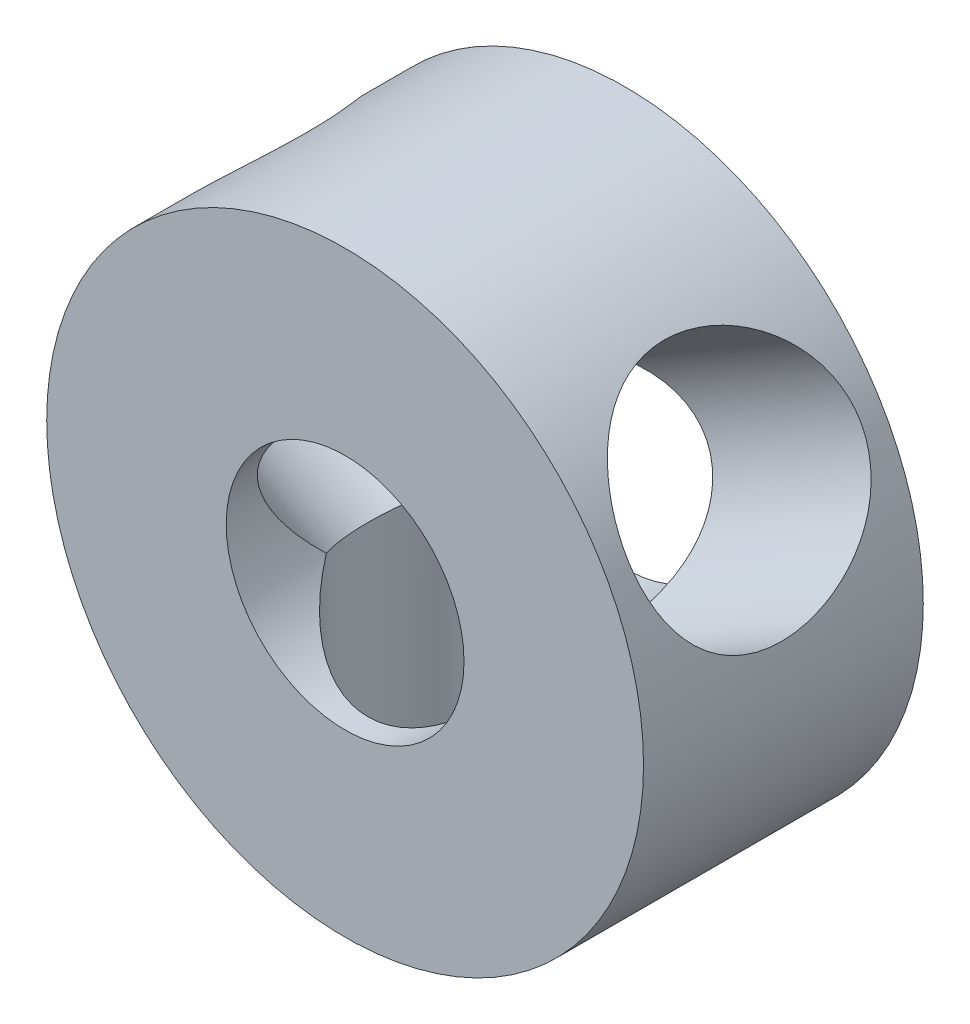
SolidWorks part; units mm, degrees
material "Plain Carbon Steel"
ref_plane "Front Plane" through (0, 0, 0) normal (0, 0, 1) x (1, 0, 0)
ref_plane "Top Plane" through (0, 0, 0) normal (0, 1, 0) x (1, 0, 0)
ref_plane "Right Plane" through (0, 0, 0) normal (1, 0, 0) x (0, 0, -1)
sketch "Sketch1" plane through (0, 0, 0) normal (0, 0, 1) x (1, 0, 0)
  circle A0 centre (0, 0) radius 32
  circle A1 centre (0, 0) radius 12.75
  dimension "D1" = 64
  dimension "D2" = 25.5
extrude "Boss-Extrude1" add sketch "Sketch1" along normal mid plane 30
sketch "Sketch2" plane through (0, 0, 0) normal (0, 1, 0) x (1, 0, 0)
  circle A0 centre (0, 0) radius 12.55
  dimension "D1" = 25.1
extrude "Cut-Extrude1" cut sketch "Sketch2" against normal through all
pattern_circular "CirPattern1" count 3 over 360 about axis through (0, 0, 15) along (0, 0, -1) of "Cut-Extrude1"
